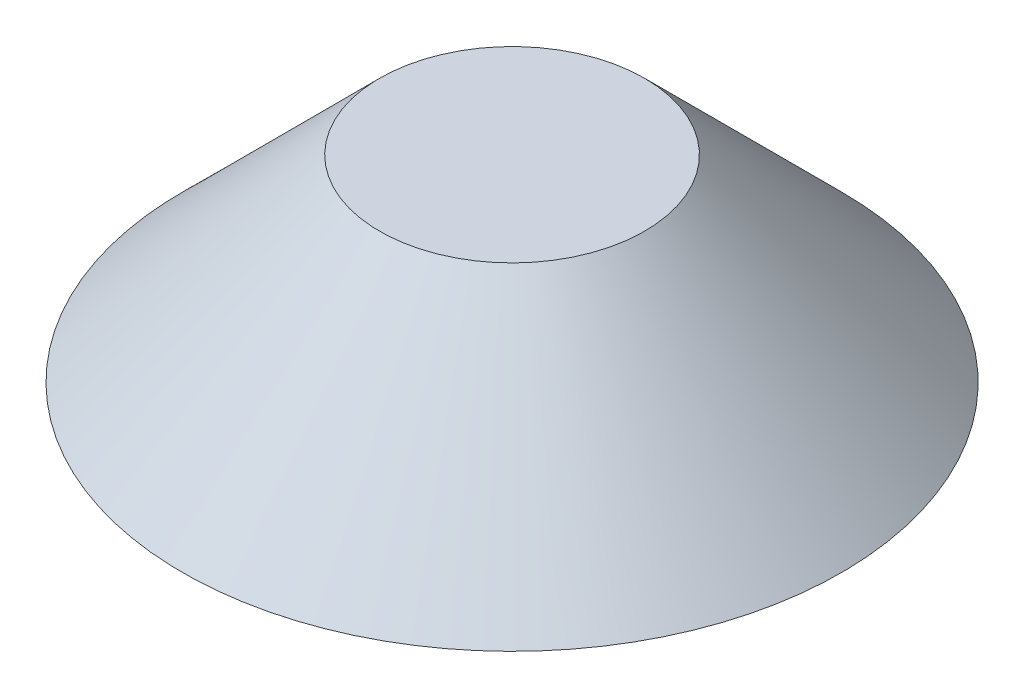
SolidWorks part; units mm, degrees
ref_plane "Front Plane" through (0, 0, 0) normal (0, 0, 1) x (1, 0, 0)
ref_plane "Top Plane" through (0, 0, 0) normal (0, 1, 0) x (1, 0, 0)
ref_plane "Right Plane" through (0, 0, 0) normal (1, 0, 0) x (0, 0, -1)
sketch "Sketch4" plane through (0, 0, 0) normal (1, 0, 0) x (0, 0, -1)
  line L0 (0, 0) -> (-12.5, 0)
  line L1 (-12.5, 0) -> (-5.0259, 7.4741)
  line L2 (0, 0) -> (0, 7.4741)
  line L3 (0, 7.4741) -> (-5.0259, 7.4741)
  line L4 (-11.7792, 0.7208) -> (-11.2194, 0) construction
  point P3 (-5.0259, 7.5)
  point P4 (-5.0848, 7.4152)
revolve "Revolve1" add sketch "Sketch4" angle 360 about L2
